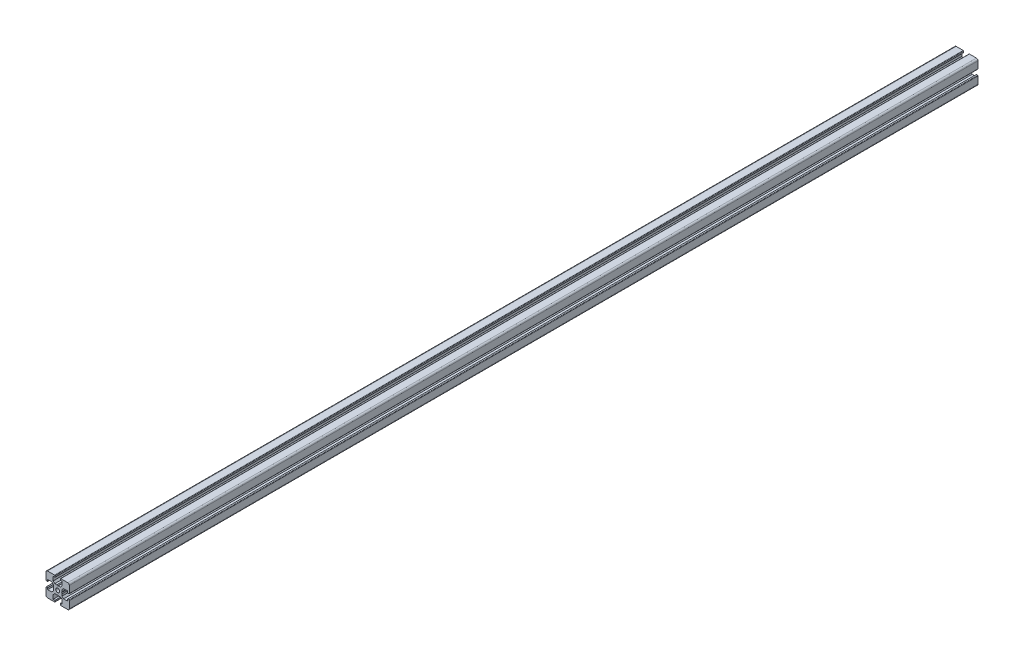
SolidWorks part; units mm, degrees
material "6061-T6 (SS)"
ref_plane "Front Plane" through (0, 0, 0) normal (0, 0, 1) x (1, 0, 0)
ref_plane "Top Plane" through (0, 0, 0) normal (0, 1, 0) x (1, 0, 0)
ref_plane "Right Plane" through (0, 0, 0) normal (1, 0, 0) x (0, 0, -1)
ref_plane "Plane1" through (0, 0, 114.5) normal (0, 0, 1) x (1, 0, 0)
sketch "Sketch1" plane through (0, 0, 114.5) normal (0, 0, 1) x (1, 0, 0)
  line L0 (-7.5, 6.5) -> (-7.5, 2)
  line L1 (-7.2, 1.7) -> (-6.4, 1.7)
  line L2 (-6.4, 1.7) -> (-6.4, 2.85)
  line L3 (-6.4, 2.85) -> (-3.8, 2.85)
  line L4 (-3.8, 2.85) -> (-2.8, 1.85)
  line L5 (-2.8, 1.85) -> (-2.8, 0.5196)
  line L6 (-2.8, 0.5196) -> (-2.5, 0)
  line L7 (-2.5, 0) -> (-2.8, -0.5196)
  line L8 (-2.8, -0.5196) -> (-2.8, -1.85)
  line L9 (-2.8, -1.85) -> (-3.8, -2.85)
  line L10 (-3.8, -2.85) -> (-6.4, -2.85)
  line L11 (-6.4, -2.85) -> (-6.4, -1.7)
  line L12 (-6.4, -1.7) -> (-7.2, -1.7)
  line L13 (-7.5, -2) -> (-7.5, -6.5)
  line L14 (-6.5, -7.5) -> (-2, -7.5)
  line L15 (-1.7, -7.2) -> (-1.7, -6.4)
  line L16 (-1.7, -6.4) -> (-2.85, -6.4)
  line L17 (-2.85, -6.4) -> (-2.85, -3.8)
  line L18 (-2.85, -3.8) -> (-1.85, -2.8)
  line L19 (-1.85, -2.8) -> (-0.5196, -2.8)
  line L20 (-0.5196, -2.8) -> (0, -2.5)
  line L21 (0, -2.5) -> (0.5196, -2.8)
  line L22 (0.5196, -2.8) -> (1.85, -2.8)
  line L23 (1.85, -2.8) -> (2.85, -3.8)
  line L24 (2.85, -3.8) -> (2.85, -6.4)
  line L25 (2.85, -6.4) -> (1.7, -6.4)
  line L26 (1.7, -6.4) -> (1.7, -7.2)
  line L27 (2, -7.5) -> (6.5, -7.5)
  line L28 (7.5, -6.5) -> (7.5, -2)
  line L29 (7.2, -1.7) -> (6.4, -1.7)
  line L30 (6.4, -1.7) -> (6.4, -2.85)
  line L31 (6.4, -2.85) -> (3.8, -2.85)
  line L32 (3.8, -2.85) -> (2.8, -1.85)
  line L33 (2.8, -1.85) -> (2.8, -0.5196)
  line L34 (2.8, -0.5196) -> (2.5, 0)
  line L35 (2.5, 0) -> (2.8, 0.5196)
  line L36 (2.8, 0.5196) -> (2.8, 1.85)
  line L37 (2.8, 1.85) -> (3.8, 2.85)
  line L38 (3.8, 2.85) -> (6.4, 2.85)
  line L39 (6.4, 2.85) -> (6.4, 1.7)
  line L40 (6.4, 1.7) -> (7.2, 1.7)
  line L41 (7.5, 2) -> (7.5, 6.5)
  line L42 (6.5, 7.5) -> (2, 7.5)
  line L43 (1.7, 7.2) -> (1.7, 6.4)
  line L44 (1.7, 6.4) -> (2.85, 6.4)
  line L45 (2.85, 6.4) -> (2.85, 3.8)
  line L46 (2.85, 3.8) -> (1.85, 2.8)
  line L47 (1.85, 2.8) -> (0.5196, 2.8)
  line L48 (0.5196, 2.8) -> (0, 2.5)
  line L49 (0, 2.5) -> (-0.5196, 2.8)
  line L50 (-0.5196, 2.8) -> (-1.85, 2.8)
  line L51 (-1.85, 2.8) -> (-2.85, 3.8)
  line L52 (-2.85, 3.8) -> (-2.85, 6.4)
  line L53 (-2.85, 6.4) -> (-1.7, 6.4)
  line L54 (-1.7, 6.4) -> (-1.7, 7.2)
  line L55 (-2, 7.5) -> (-6.5, 7.5)
  circle A0 centre (0, 0) radius 1.25
  arc A1 (-7.5, 2) -> (-7.2, 1.7) centre (-7.2, 2) ccw
  arc A2 (-7.2, -1.7) -> (-7.5, -2) centre (-7.2, -2) ccw
  arc A3 (-7.5, -6.5) -> (-6.5, -7.5) centre (-6.5, -6.5) ccw
  arc A4 (-2, -7.5) -> (-1.7, -7.2) centre (-2, -7.2) ccw
  arc A5 (1.7, -7.2) -> (2, -7.5) centre (2, -7.2) ccw
  arc A6 (6.5, -7.5) -> (7.5, -6.5) centre (6.5, -6.5) ccw
  arc A7 (7.5, -2) -> (7.2, -1.7) centre (7.2, -2) ccw
  arc A8 (7.2, 1.7) -> (7.5, 2) centre (7.2, 2) ccw
  arc A9 (7.5, 6.5) -> (6.5, 7.5) centre (6.5, 6.5) ccw
  arc A10 (2, 7.5) -> (1.7, 7.2) centre (2, 7.2) ccw
  arc A11 (-1.7, 7.2) -> (-2, 7.5) centre (-2, 7.2) ccw
  arc A12 (-6.5, 7.5) -> (-7.5, 6.5) centre (-6.5, 6.5) ccw
extrude "Boss-Extrude1" add sketch "Sketch1" against normal blind 584.45
